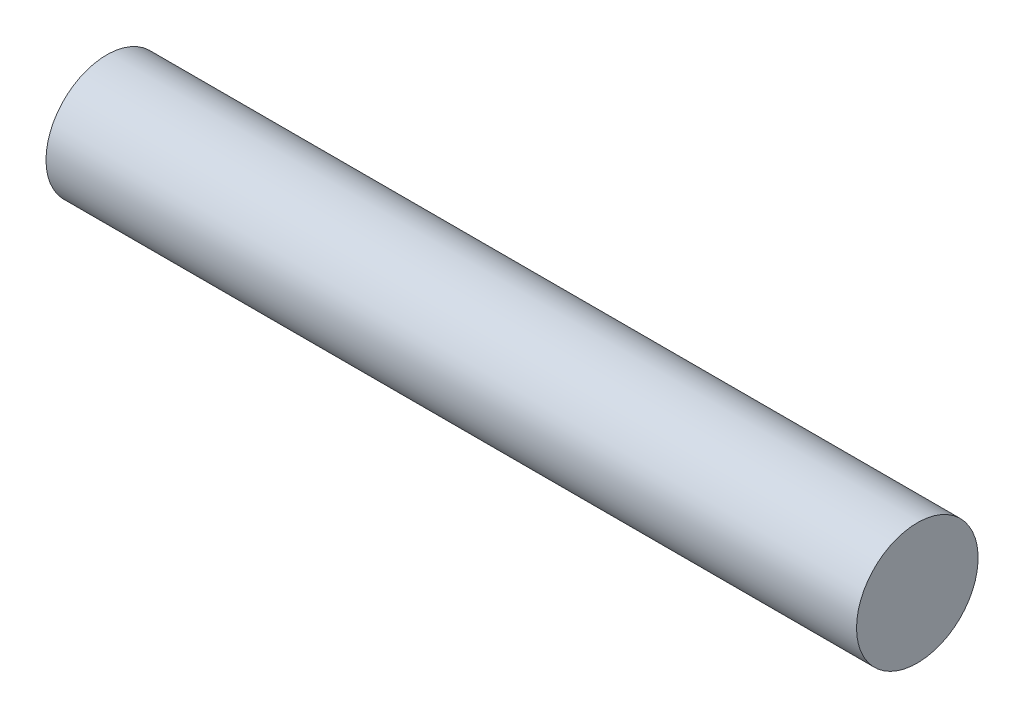
SolidWorks part; units mm, degrees
ref_plane "Front Plane" through (0, 0, 0) normal (0, 0, 1) x (1, 0, 0)
ref_plane "Top Plane" through (0, 0, 0) normal (0, 1, 0) x (1, 0, 0)
ref_plane "Right Plane" through (0, 0, 0) normal (1, 0, 0) x (0, 0, -1)
sketch "Sketch1" plane through (0, 0, 0) normal (0, 1, 0) x (1, 0, 0)
  line L0 (0, 0) -> (152.4, 0)
  line L5 (0, 0) -> (-38.1, 0)
  line L6 (152.4, 0) -> (190.5, 0)
  line L7 (-38.1, 0) -> (-38.1, -34.29)
  line L8 (-38.1, -34.29) -> (190.5, -34.29)
  line L9 (190.5, -34.29) -> (190.5, 0)
  line L10 (39.37, 0) -> (0, 0)
  line L11 (-38.1, -17.145) -> (190.5, -17.145) construction
  dimension "D4" = 152.4
  dimension "D5" = 38.1
  dimension "D6" = 38.1
  dimension "D7" = 34.29
  dimension "D8" = 39.37
revolve "Revolve2" add sketch "Sketch1" angle 360 about L11
